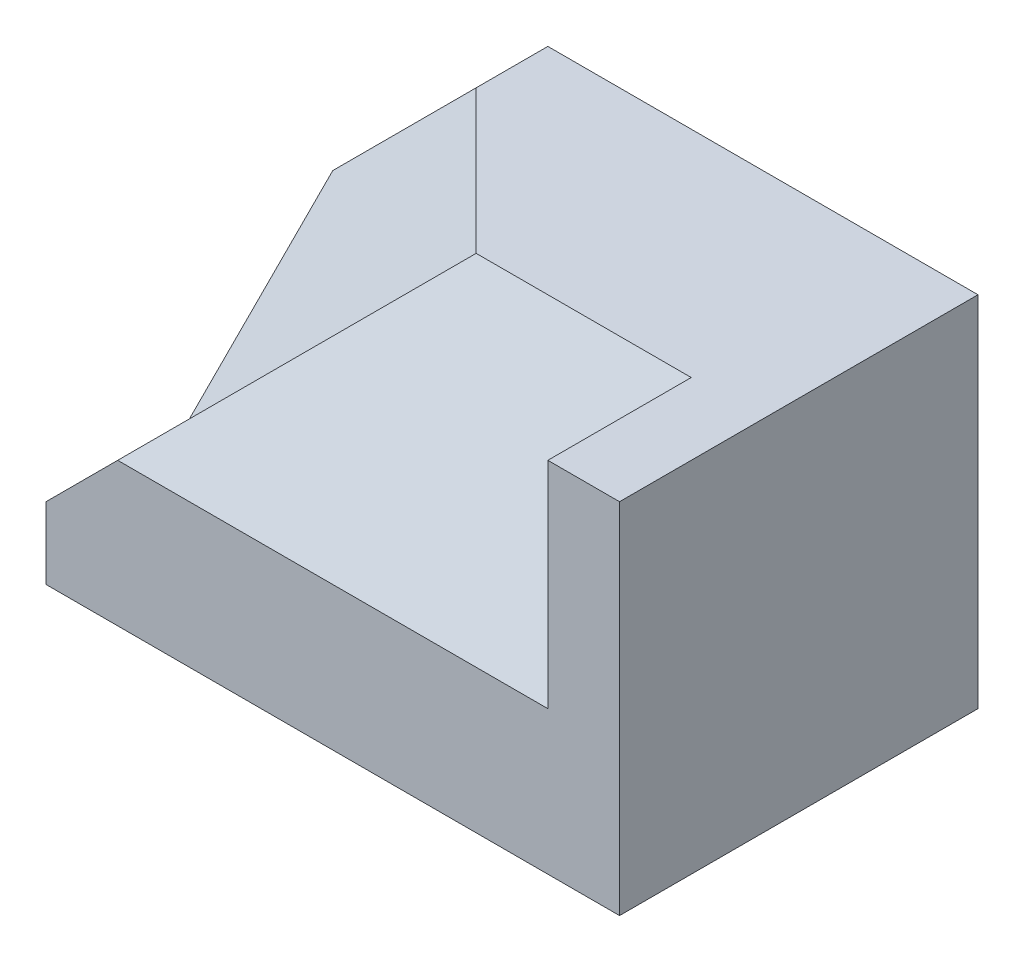
SolidWorks part; units mm, degrees
ref_plane "Front" through (0, 0, 0) normal (0, 0, 1) x (1, 0, 0)
ref_plane "Top" through (0, 0, 0) normal (0, 1, 0) x (1, 0, 0)
ref_plane "Right" through (0, 0, 0) normal (1, 0, 0) x (0, 0, -1)
sketch "Sketch1" plane through (0, 0, 0) normal (0, 0, 1) x (1, 0, 0)
  line L0 (-4, 0.5) -> (-2, 2.5)
  line L1 (-4, -2.5) -> (4, -2.5)
  line L2 (-4, -2.5) -> (-4, 0.5)
  line L3 (-2, 2.5) -> (4, 2.5)
  line L4 (4, -2.5) -> (4, 2.5)
  line L5 (-4, -2.5) -> (4, 2.5) construction
  line L6 (-4, 2.5) -> (4, -2.5) construction
  point P0 (0, 0)
  dimension "D1" = 8
  dimension "D2" = 5
extrude "Boss-Extrude1" add sketch "Sketch1" along normal blind 3
sketch3d "3DSketch1"
  line L0 (-4, 0.5, 3) -> (-4, 0.5, 0) construction
  line L1 (-2, 2.5, 3) -> (-2, 2.5, 0) construction
  line L2 (-4, 0.5, 3) -> (-4, -2.5, 3) construction
  line L3 (4, 2.5, 0) -> (-2, 2.5, 0) construction
  line L4 (-4, -1.5, 3) -> (-4, 0.5, 1)
  line L5 (-4, 0.5, 1) -> (-2, 2.5, 1)
  line L8 (0, 2.5, 3) -> (-4, -1.5, 3)
  line L9 (0, 2.5, 3) -> (-2, 2.5, 1)
  point P0 (-4, 0.5, 1)
  point P1 (-2, 2.5, 1)
  point P4 (-4, -1.5, 3)
  point P7 (0, 2.5, 3)
  point P14 (-1.3231, -0.8785, 3)
  dimension "D1" = 1
  dimension "D2" = 1
  dimension "D3" = 2
  dimension "D4" = 3
  dimension "D5" = 1
extrude "Cut-Extrude2" cut sketch "3DSketch1" along direction (0.7071, -0.7071, 0) on the side of the normal blind 1 contours L8 L4 L5 L9
sketch "Sketch2" plane through (0, 0, 3) normal (0, 0, 1) x (1, 0, 0)
  line L0 (4, 2.5) -> (3, 2.5)
  line L1 (4, 2.5) -> (0, 2.5) construction
  line L2 (3, 2.5) -> (3, -0.5)
  line L3 (3, -0.5) -> (-3, -0.5)
  line L4 (0, 2.5) -> (-4, -1.5) construction
  line L5 (-3, -0.5) -> (-4, -1.5)
  line L6 (-4, -1.5) -> (-4, -2.5)
  line L7 (-4, -2.5) -> (4, -2.5)
  line L8 (4, -2.5) -> (4, 2.5)
  dimension "D1" = 1
  dimension "D2" = 1
extrude "Boss-Extrude2" add sketch "Sketch2" along normal blind 2
sketch "Sketch3" plane through (0, 0, 3) normal (0, 0, 1) x (1, 0, 0)
  line L0 (3, 2.5) -> (3, -0.5) construction
  line L5 (-3, -0.5) -> (3, -0.5)
  line L8 (3, -0.5) -> (3, 2.5)
  line L9 (3, 2.5) -> (0, 2.5) construction
  line L10 (0, 2.5) -> (3, 2.5)
  line L11 (-3, -0.5) -> (0, 2.5)
extrude "Boss-Extrude3" add sketch "Sketch3" along normal blind 2
sketch3d "3DSketch3"
  line L0 (0, 2.5, 5) -> (-4, -1.5, 5) construction
  line L1 (-4, -0.5, 5) -> (0, 2.5, 3)
  line L2 (0, 2.5, 3) -> (3, 2.5, 3)
  line L3 (4, 2.5, 5) -> (4, 2.5, 0) construction
  line L4 (4, 2.5, 0) -> (-2, 2.5, 0) construction
  line L5 (4, -2.5, 5) -> (4, 2.5, 5) construction
  line L6 (4, 2.5, 5) -> (0, 2.5, 5) construction
  line L8 (3, 2.5, 3) -> (3, -0.5, 5)
  line L9 (3, -0.5, 5) -> (-4, -0.5, 5)
  point P0 (-3, -0.5, 5)
  point P1 (3, -0.5, 5)
  point P4 (0, 2.5, 3)
  point P16 (3, 2.5, 3)
  point P18 (1, 2.5, 3)
  dimension "D1" = 4
  dimension "D2" = 3
  dimension "D3" = 1
  dimension "D4" = 3
  dimension "D5" = 1
  dimension "D6" = 1
  dimension "D7" = 3
extrude "Cut-Extrude3" cut sketch "3DSketch3" along direction (0, -1, 0) on the side against the normal blind 3
